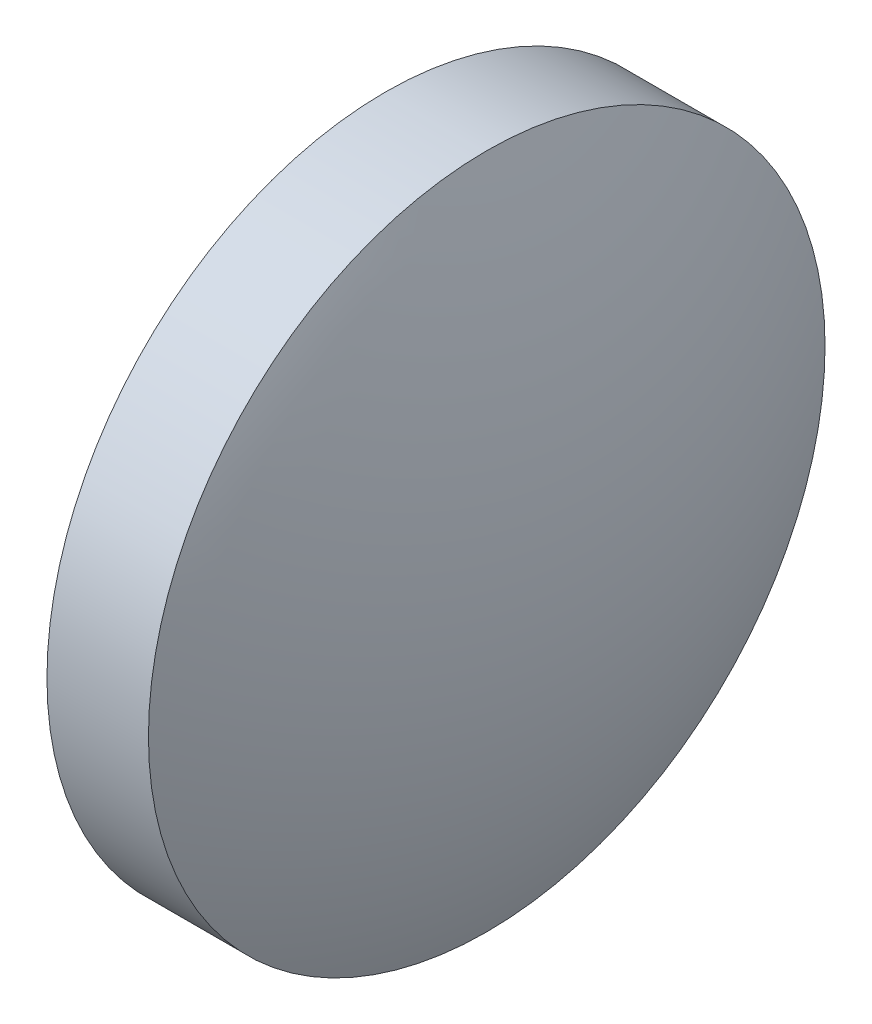
SolidWorks part; units mm, degrees
ref_plane "前视基准面" through (0, 0, 0) normal (0, 0, 1) x (1, 0, 0)
ref_plane "上视基准面" through (0, 0, 0) normal (0, 1, 0) x (1, 0, 0)
ref_plane "右视基准面" through (0, 0, 0) normal (1, 0, 0) x (0, 0, -1)
sketch "草图1" plane through (0, 0, 0) normal (0, 0, 1) x (1, 0, 0)
  line L0 (233.0206, 168.9814) -> (243.5206, 168.9814)
  line L1 (243.5206, 168.9814) -> (243.5206, 98.9814)
  line L2 (243.5206, 98.9814) -> (233.0206, 98.9814)
  line L3 (233.0206, 98.9814) -> (233.0206, 168.9814)
  line L4 (222.8966, 133.9814) -> (254.7695, 133.9814) construction
  arc A0 (233.0206, 168.9814) -> (233.0206, 98.9814) centre (311.4967, 133.9814) ccw
  arc A1 (243.5206, 98.9814) -> (243.5206, 168.9814) centre (165.0445, 133.9814) ccw
revolve "旋转1" add sketch "草图1" angle 360 about L4
